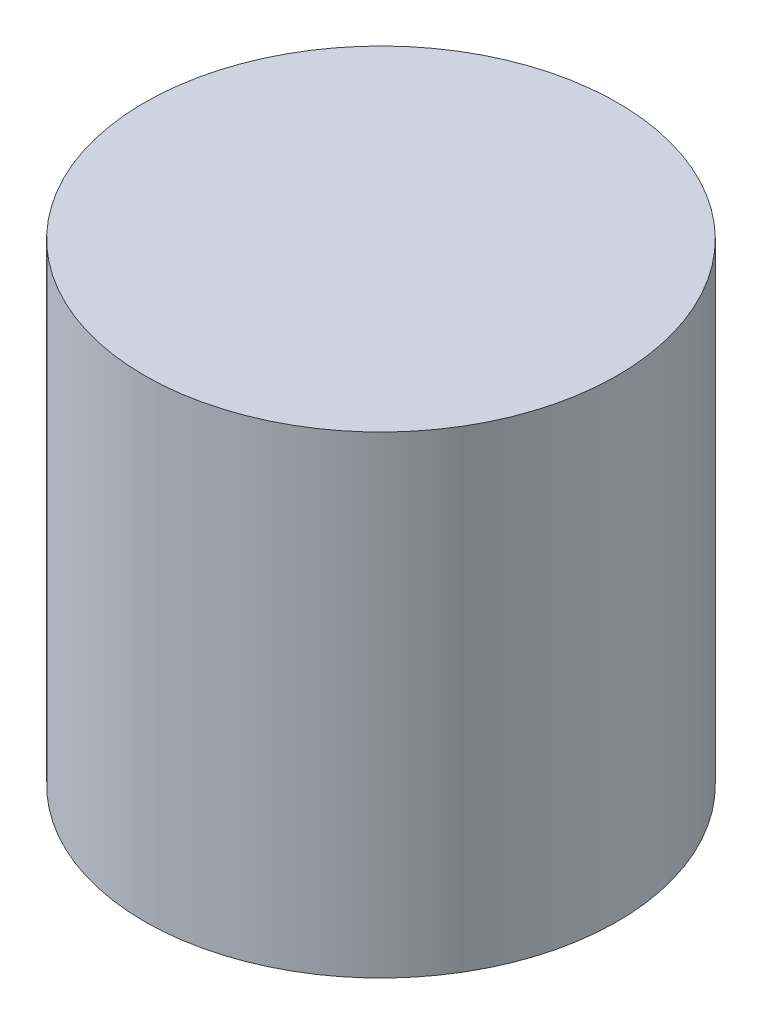
SolidWorks part; units mm, degrees
ref_plane "Front Plane" through (0, 0, 0) normal (0, 0, 1) x (1, 0, 0)
ref_plane "Top Plane" through (0, 0, 0) normal (0, 1, 0) x (1, 0, 0)
ref_plane "Right Plane" through (0, 0, 0) normal (1, 0, 0) x (0, 0, -1)
sketch "Sketch1" plane through (0, 0, 0) normal (0, 1, 0) x (1, 0, 0)
  circle A0 centre (-46.1015, 11.4538) radius 63.5
  dimension "D1" = 127
extrude "Boss-Extrude1" add sketch "Sketch1" along normal blind 127
